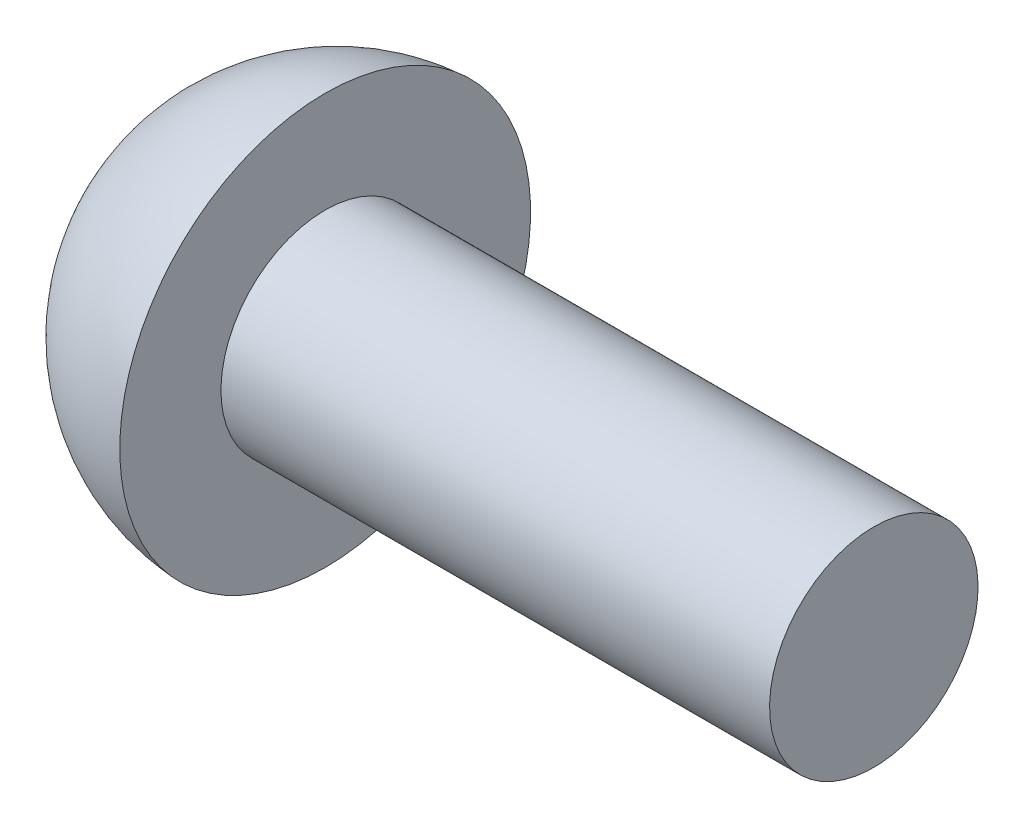
SolidWorks part; units mm, degrees
material "Alloy Steel"
ref_plane "Front Plane" through (0, 0, 0) normal (0, 0, 1) x (1, 0, 0)
ref_plane "Top Plane" through (0, 0, 0) normal (0, 1, 0) x (1, 0, 0)
ref_plane "Right Plane" through (0, 0, 0) normal (1, 0, 0) x (0, 0, -1)
sketch "Sketch2" plane through (0, 0, 0) normal (0, 0, 1) x (1, 0, 0)
  line L0 (-6.35, 4.7549) -> (-6.35, 2.413)
  line L3 (-6.35, 2.413) -> (6.35, 2.413)
  line L4 (6.35, 0) -> (6.35, 2.413)
  line L5 (0, 0) -> (6.35, 2.413) construction
  line L6 (-6.35, 2.413) -> (0, 0) construction
  line L7 (6.35, 0) -> (-10.8433, 0)
  arc A0 (-6.35, 4.7549) -> (-10.8433, 0) centre (-6.0808, 0) ccw
  point P0 (0, 0)
  point P9 (-6.35, 1.2065)
  dimension "D3" = 4.7625
  dimension "D2" = 12.7
revolve "Revolve8" add sketch "Sketch2" angle 360 about L7
